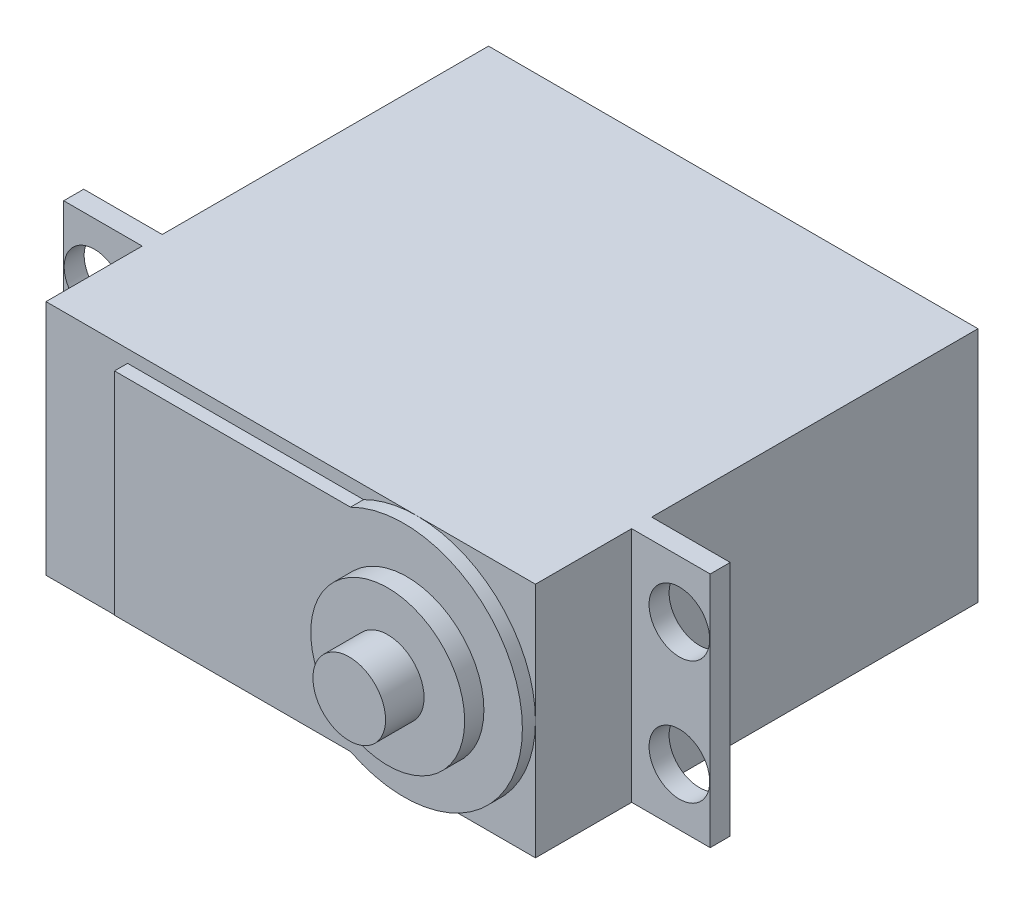
SolidWorks part; units mm, degrees
material "Nylon 101"
ref_plane "Front Plane" through (0, 0, 0) normal (0, 0, 1) x (1, 0, 0)
ref_plane "Top Plane" through (0, 0, 0) normal (0, 1, 0) x (1, 0, 0)
ref_plane "Right Plane" through (0, 0, 0) normal (1, 0, 0) x (0, 0, -1)
sketch "Sketch3" plane through (0, 0, 0) normal (0, 0, 1) x (1, 0, 0)
  line L1 (-73.7676, -3.1881) -> (-33.3816, -3.1881)
  line L2 (-73.7676, -3.1881) -> (-73.7676, -22.7461)
  line L3 (-73.7676, -22.7461) -> (-33.3816, -22.7461)
  line L4 (-33.3816, -3.1881) -> (-33.3816, -22.7461)
extrude "Boss-Extrude2" add sketch "Sketch3" along normal blind 26.924
sketch "Sketch4" plane through (0, 0, 26.924) normal (0, 0, 1) x (1, 0, 0)
  line L0 (-73.7676, -3.1881) -> (-73.7676, -22.7461) construction
  line L1 (-80.2446, -3.1881) -> (-26.9046, -3.1881)
  line L2 (-80.2446, -3.1881) -> (-80.2446, -22.7461)
  line L3 (-80.2446, -22.7461) -> (-26.9046, -22.7461)
  line L4 (-26.9046, -3.1881) -> (-26.9046, -22.7461)
  line L5 (-33.3816, -22.7461) -> (-33.3816, -3.1881) construction
  dimension "D1" = 6.477
  dimension "D2" = 6.477
extrude "Boss-Extrude3" add sketch "Sketch4" along normal blind 1.651
sketch "Sketch5" plane through (0, 0, 28.575) normal (0, 0, 1) x (1, 0, 0)
  line L0 (-80.2446, -3.1881) -> (-80.2446, -22.7461) construction
  line L1 (-26.9046, -3.1881) -> (-80.2446, -3.1881) construction
  circle A0 centre (-77.7046, -7.8871) radius 2.5019
  circle A1 centre (-29.4446, -7.8871) radius 2.5019
  circle A2 centre (-29.4446, -18.0471) radius 2.5019
  circle A3 centre (-77.7046, -18.0471) radius 2.5019
  dimension "D1" = 2.54
  dimension "D2" = 4.699
  dimension "D3" = 2
  dimension "D4" = 2
extrude "Cut-Extrude1" cut sketch "Sketch5" against normal blind 3.175
sketch "Sketch6" plane through (0, 0, 28.575) normal (0, 0, 1) x (1, 0, 0)
  line L1 (-73.7676, -3.1881) -> (-33.3816, -3.1881)
  line L2 (-73.7676, -3.1881) -> (-73.7676, -22.7461)
  line L3 (-73.7676, -22.7461) -> (-33.3816, -22.7461)
  line L4 (-33.3816, -3.1881) -> (-33.3816, -22.7461)
extrude "Boss-Extrude4" add sketch "Sketch6" along normal blind 7.9375
sketch "Sketch7" plane through (0, 0, 36.5125) normal (0, 0, 1) x (1, 0, 0)
  line L3 (-43.1606, -3.1881) -> (-43.1606, -4.2358)
  line L7 (-67.0366, -21.6983) -> (-67.0366, -4.2358)
  line L9 (-47.5645, -21.6983) -> (-67.0366, -21.6983)
  line L10 (-47.5645, -4.2358) -> (-67.0366, -4.2358)
  arc A0 (-47.5645, -21.6983) -> (-47.5645, -4.2358) centre (-43.1606, -12.9671) ccw
extrude "Boss-Extrude5" add sketch "Sketch7" along normal blind 1.0795
sketch "Sketch8" plane through (0, 0, 37.592) normal (0, 0, 1) x (1, 0, 0)
  line L0 (-33.3816, -22.7461) -> (-33.3816, -3.1881) construction
  line L1 (-43.1606, -22.7461) -> (-33.3816, -22.7461) construction
  circle A0 centre (-42.9066, -13.2211) radius 6.35
  dimension "D1" = 9.525
  dimension "D2" = 9.525
extrude "Boss-Extrude6" add sketch "Sketch8" along normal blind 1.5875
sketch "Sketch10" plane through (0, 0, 39.1795) normal (0, 0, 1) x (1, 0, 0)
  circle A0 centre (-42.9066, -13.2211) radius 2.9972
extrude "Boss-Extrude7" add sketch "Sketch10" along normal blind 3.175
